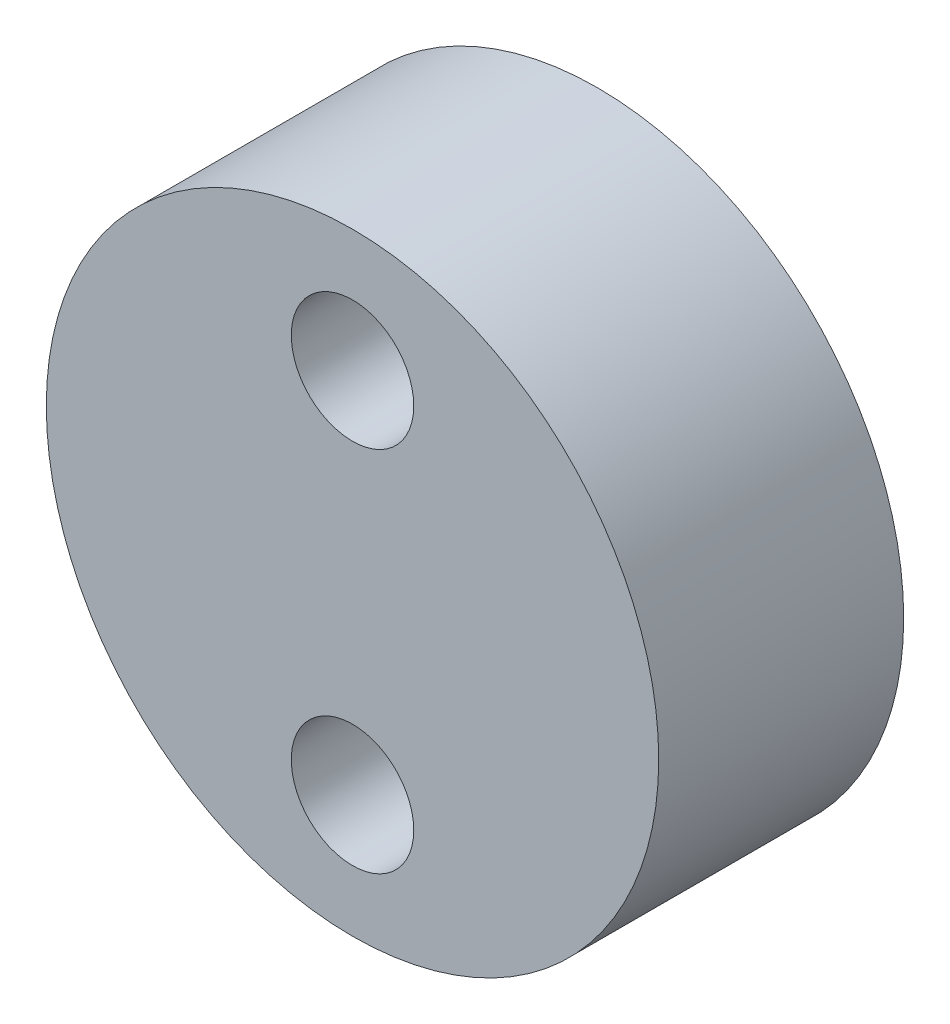
SolidWorks part; units mm, degrees
ref_plane "Front Plane" through (0, 0, 0) normal (0, 0, 1) x (1, 0, 0)
ref_plane "Top Plane" through (0, 0, 0) normal (0, 1, 0) x (1, 0, 0)
ref_plane "Right Plane" through (0, 0, 0) normal (1, 0, 0) x (0, 0, -1)
sketch "Sketch2" plane through (0, 0, 0) normal (0, 0, 1) x (1, 0, 0)
  circle A0 centre (0, 0) radius 25
  circle A1 centre (0, 15) radius 5
  circle A2 centre (0, -15) radius 5
  point P7 (0, 0)
  point P8 (0, 0)
  point P9 (0, 0)
  point P10 (0, 0)
  dimension "D1" = 50
  dimension "D4" = 10
  dimension "D2" = 15
  dimension "D3" = 30
extrude "Boss-Extrude1" add sketch "Sketch2" along normal blind 20
